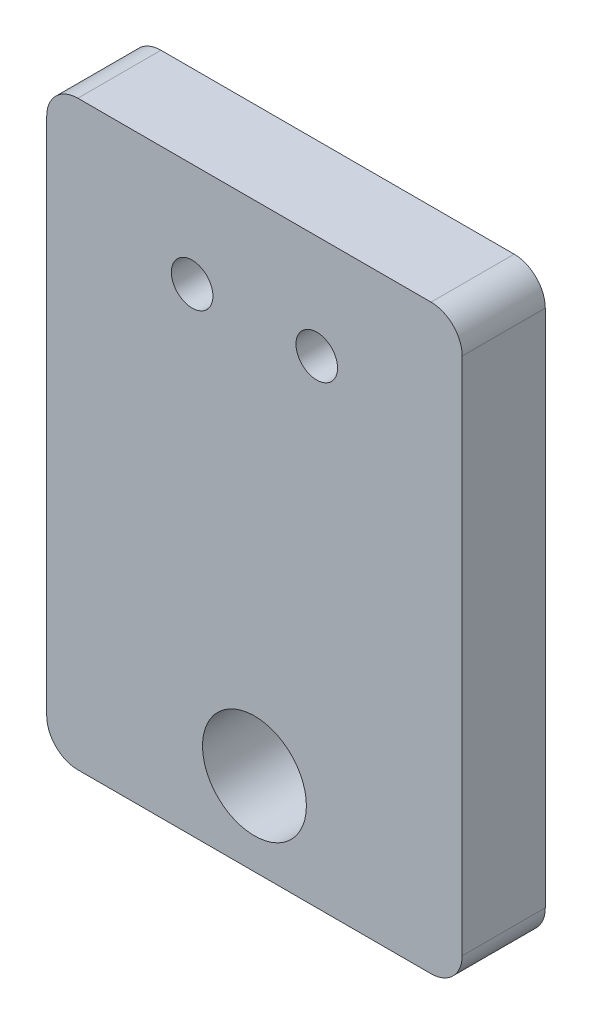
SolidWorks part; units mm, degrees
ref_plane "Front" through (0, 0, 0) normal (0, 0, 1) x (1, 0, 0)
ref_plane "Top" through (0, 0, 0) normal (0, 1, 0) x (1, 0, 0)
ref_plane "Right" through (0, 0, 0) normal (1, 0, 0) x (0, 0, -1)
sketch "Sketch1" plane through (0, 0, 0) normal (0, 0, 1) x (1, 0, 0)
  line L0 (0, 11.6405) -> (0, -4.4679) construction
  line L1 (-8.5, 14) -> (8.5, 14)
  line L2 (-10, 12.5) -> (-10, -12.5)
  line L3 (-8.5, -14) -> (8.5, -14)
  line L4 (10, 12.5) -> (10, -12.5)
  line L5 (-10, 14) -> (10, -14) construction
  line L6 (-10, -14) -> (10, 14) construction
  circle A0 centre (0, -10) radius 2.5
  circle A1 centre (-3, 9) radius 1
  circle A2 centre (3, 9) radius 1
  arc A3 (-10, -12.5) -> (-8.5, -14) centre (-8.5, -12.5) ccw
  arc A4 (8.5, -14) -> (10, -12.5) centre (8.5, -12.5) ccw
  arc A5 (8.5, 14) -> (10, 12.5) centre (8.5, 12.5) cw
  arc A6 (-8.5, 14) -> (-10, 12.5) centre (-8.5, 12.5) ccw
  point P0 (0, 0)
  dimension "D3" = 3
  dimension "D6" = 1.5
  dimension "D1" = 20
  dimension "D2" = 28
  dimension "D4" = 4
  dimension "D5" = 5
extrude "Boss-Extrude1" add sketch "Sketch1" along normal blind 4
